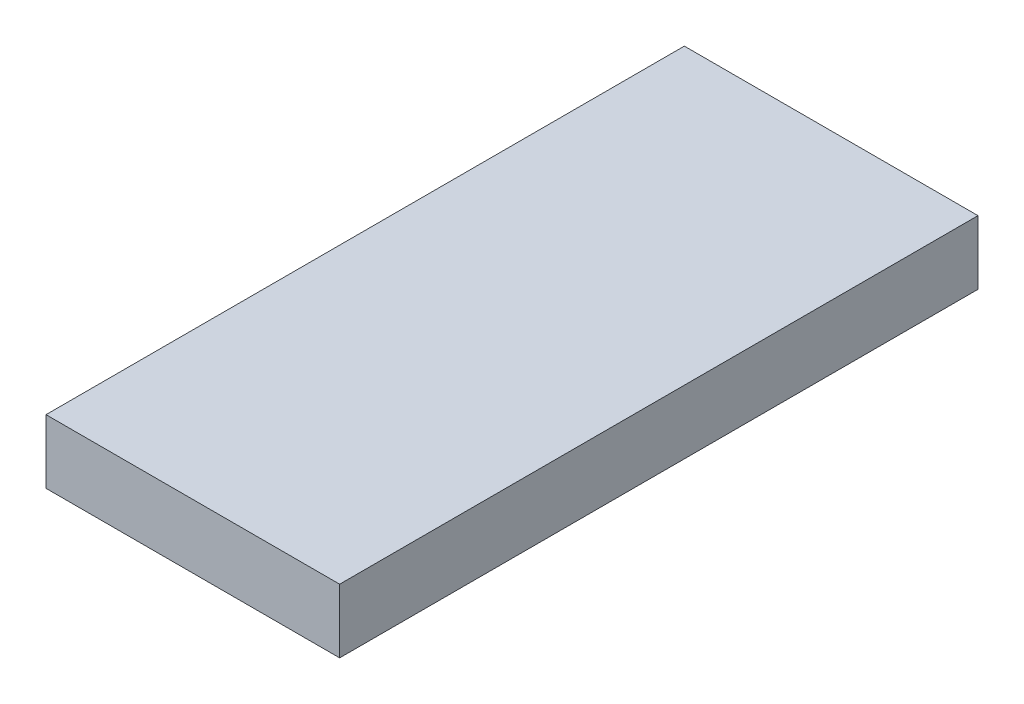
SolidWorks part; units mm, degrees
ref_plane "Front Plane" through (0, 0, 0) normal (0, 0, 1) x (1, 0, 0)
ref_plane "Top Plane" through (0, 0, 0) normal (0, 1, 0) x (1, 0, 0)
ref_plane "Right Plane" through (0, 0, 0) normal (1, 0, 0) x (0, 0, -1)
sketch "Sketch1" plane through (0, 0, 0) normal (0, 1, 0) x (1, 0, 0)
  line L1 (0, 0) -> (36.5125, 0)
  line L2 (0, 0) -> (0, 79.375)
  line L3 (0, 79.375) -> (36.5125, 79.375)
  line L4 (36.5125, 0) -> (36.5125, 79.375)
  dimension "D1" = 79.375
  dimension "D2" = 36.5125
extrude "Boss-Extrude1" add sketch "Sketch1" along normal blind 7.9375
